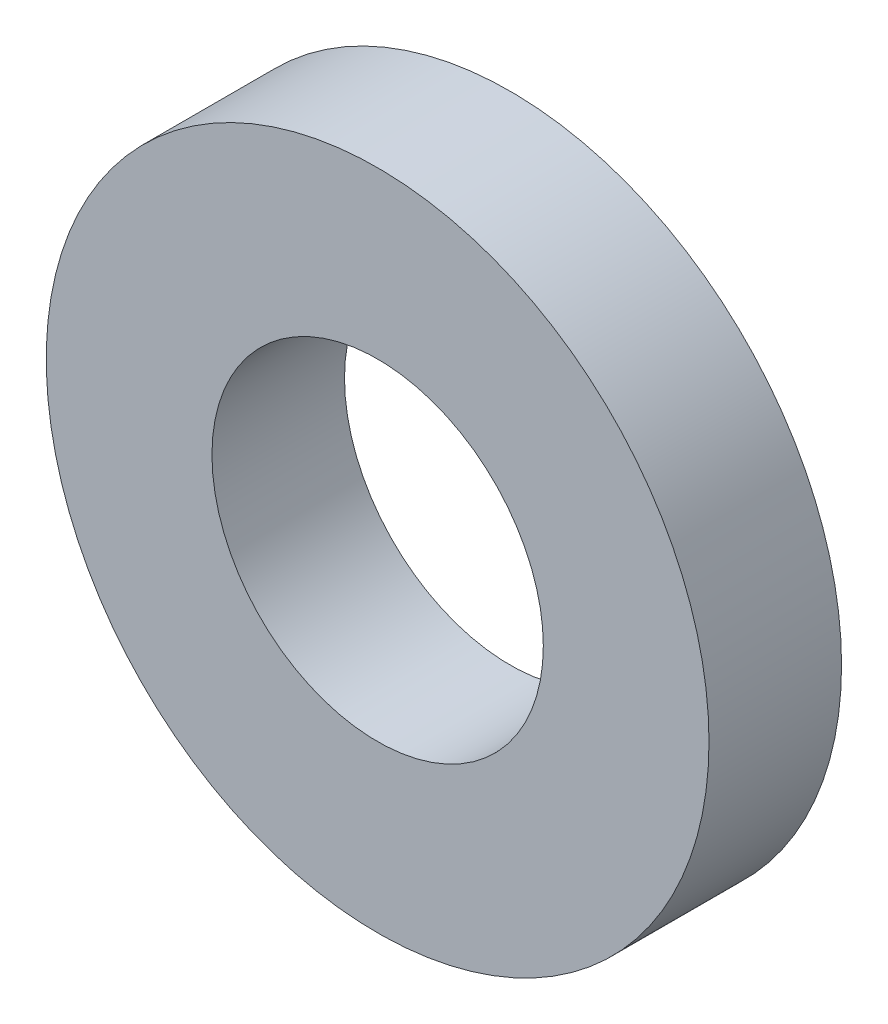
SolidWorks part; units mm, degrees
ref_plane "Front Plane" through (0, 0, 0) normal (0, 0, 1) x (1, 0, 0)
ref_plane "Top Plane" through (0, 0, 0) normal (0, 1, 0) x (1, 0, 0)
ref_plane "Right Plane" through (0, 0, 0) normal (1, 0, 0) x (0, 0, -1)
sketch "Sketch1" plane through (0, 0, 0) normal (0, 0, 1) x (1, 0, 0)
  circle A0 centre (0, 0) radius 1.25
  circle A1 centre (0, 0) radius 2.5
  dimension "D1" = 2.5
  dimension "D2" = 5
extrude "Boss-Extrude1" add sketch "Sketch1" along normal blind 1
